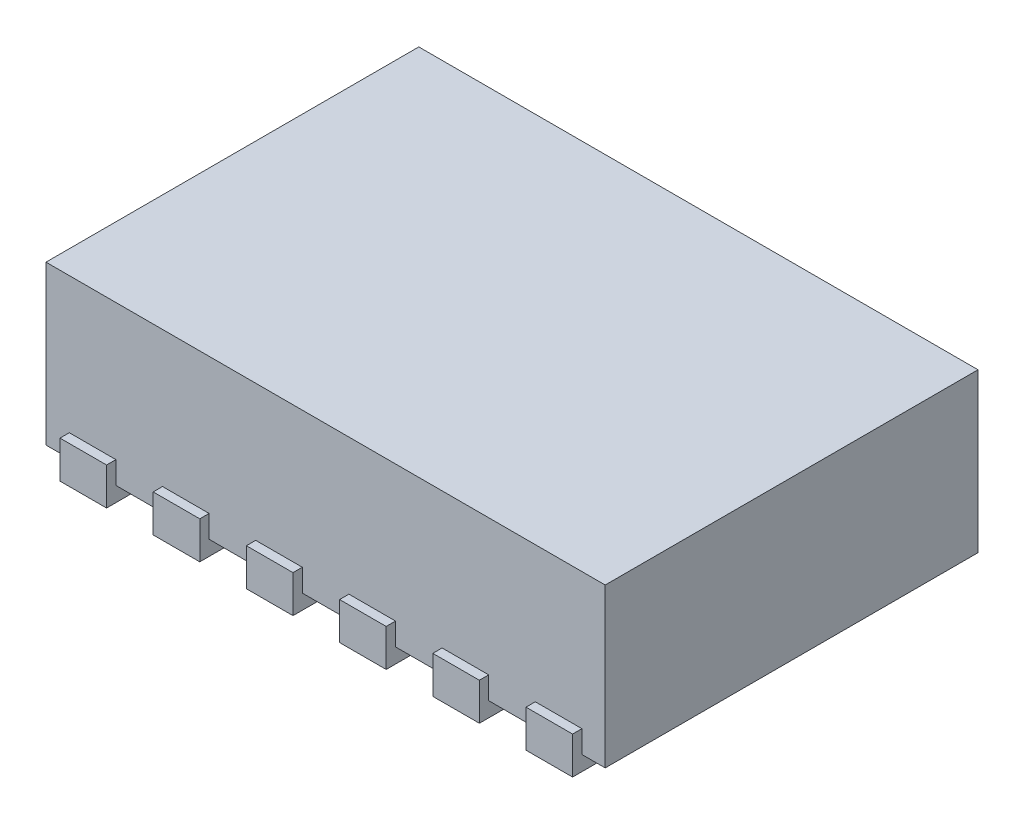
SolidWorks part; units mm, degrees
ref_plane "Front Plane" through (0, 0, 0) normal (0, 0, 1) x (1, 0, 0)
ref_plane "Top Plane" through (0, 0, 0) normal (0, 1, 0) x (1, 0, 0)
ref_plane "Right Plane" through (0, 0, 0) normal (1, 0, 0) x (0, 0, -1)
sketch "Sketch1" plane through (0, 0, 0) normal (0, 1, 0) x (1, 0, 0)
  line L0 (0, 0) -> (0, 2)
  line L1 (0, 2) -> (3, 2)
  line L2 (0, 0) -> (3, 0)
  line L3 (3, 0) -> (3, 2)
extrude "Boss-Extrude1" add sketch "Sketch1" along normal blind 0.85
sketch "Sketch2" plane through (0, 0, 0) normal (0, -1, 0) x (1, 0, 0)
  line L2 (2.5, -0.65) -> (0.5, -0.65)
  line L3 (2.375, 0.05) -> (2.125, 0.05)
  line L4 (2.125, 0.05) -> (2.125, -0.25)
  line L5 (2.125, -0.25) -> (2.375, -0.25)
  line L8 (2.375, -1.75) -> (2.125, -1.75)
  line L9 (1.875, 0.05) -> (1.625, 0.05)
  line L10 (2.5, -1.35) -> (2.5, -0.65)
  line L11 (2.875, 0.05) -> (2.625, 0.05)
  line L12 (2.625, 0.05) -> (2.625, -0.25)
  line L13 (2.625, -0.25) -> (2.875, -0.25)
  line L14 (1.625, 0.05) -> (1.625, -0.25)
  line L15 (1.625, -0.25) -> (1.875, -0.25)
  line L16 (2.375, -0.25) -> (2.375, 0.05)
  line L17 (1.875, -0.25) -> (1.875, 0.05)
  line L18 (2.125, -1.75) -> (2.125, -2.05)
  line L19 (2.125, -2.05) -> (2.375, -2.05)
  line L20 (1.875, -1.75) -> (1.625, -1.75)
  line L21 (2.875, -1.75) -> (2.625, -1.75)
  line L22 (1.375, 0.05) -> (1.125, 0.05)
  line L23 (2.625, -1.75) -> (2.625, -2.05)
  line L24 (2.625, -2.05) -> (2.875, -2.05)
  line L25 (1.125, 0.05) -> (1.125, -0.25)
  line L26 (1.125, -0.25) -> (1.375, -0.25)
  line L27 (1.375, -0.25) -> (1.375, 0.05)
  line L28 (1.625, -1.75) -> (1.625, -2.05)
  line L29 (1.625, -2.05) -> (1.875, -2.05)
  line L30 (2.375, -2.05) -> (2.375, -1.75)
  line L31 (1.875, -2.05) -> (1.875, -1.75)
  line L32 (1.375, -1.75) -> (1.125, -1.75)
  line L33 (1.125, -1.75) -> (1.125, -2.05)
  line L34 (1.125, -2.05) -> (1.375, -2.05)
  line L35 (1.375, -2.05) -> (1.375, -1.75)
  line L36 (2.875, -2.05) -> (2.875, -1.75)
  line L37 (0.875, -1.75) -> (0.625, -1.75)
  line L38 (0.625, -1.75) -> (0.625, -2.05)
  line L39 (0.625, -2.05) -> (0.875, -2.05)
  line L40 (0.875, -2.05) -> (0.875, -1.75)
  line L41 (0.375, -1.75) -> (0.125, -1.75)
  line L42 (0.125, -1.75) -> (0.125, -2.05)
  line L43 (0.125, -2.05) -> (0.375, -2.05)
  line L44 (0.375, -2.05) -> (0.375, -1.75)
  line L51 (0.6, -1.35) -> (0.5, -1.25)
  line L52 (0.5, -1.25) -> (0.5, -0.65)
  line L53 (2.875, -0.25) -> (2.875, 0.05)
  line L54 (0.6, -1.35) -> (2.5, -1.35)
  line L56 (0.875, 0.05) -> (0.625, 0.05)
  line L57 (0.625, 0.05) -> (0.625, -0.25)
  line L58 (0.625, -0.25) -> (0.875, -0.25)
  line L59 (0.875, -0.25) -> (0.875, 0.05)
  line L60 (0.375, 0.05) -> (0.125, 0.05)
  line L61 (0.125, 0.05) -> (0.125, -0.25)
  line L62 (0.125, -0.25) -> (0.375, -0.25)
  line L63 (0.375, -0.25) -> (0.375, 0.05)
extrude "Boss-Extrude2" add sketch "Sketch2" against normal blind 0.2 from offset 0.08
